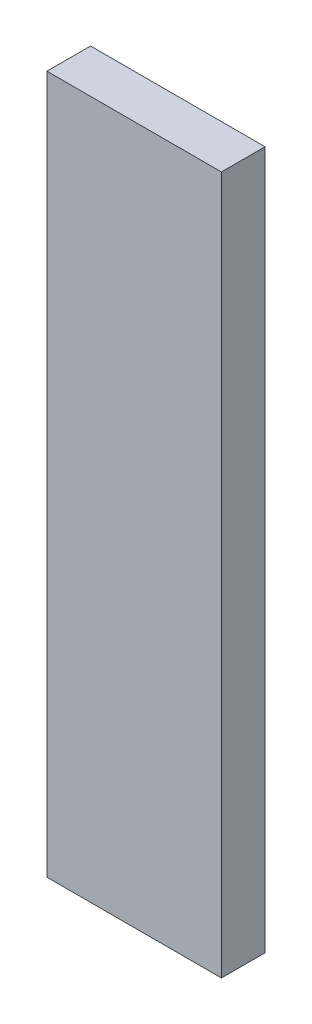
SolidWorks part; units mm, degrees
ref_plane "Front Plane" through (0, 0, 0) normal (0, 0, 1) x (1, 0, 0)
ref_plane "Top Plane" through (0, 0, 0) normal (0, 1, 0) x (1, 0, 0)
ref_plane "Right Plane" through (0, 0, 0) normal (1, 0, 0) x (0, 0, -1)
sketch "Sketch1" plane through (0, 0, 0) normal (0, 0, 1) x (1, 0, 0)
  line L1 (0, 0) -> (50.8, 0)
  line L2 (0, 0) -> (0, 203.2)
  line L3 (0, 203.2) -> (50.8, 203.2)
  line L4 (50.8, 0) -> (50.8, 203.2)
  dimension "D1" = 203.2
  dimension "D2" = 50.8
extrude "Boss-Extrude1" add sketch "Sketch1" along normal blind 12.7
